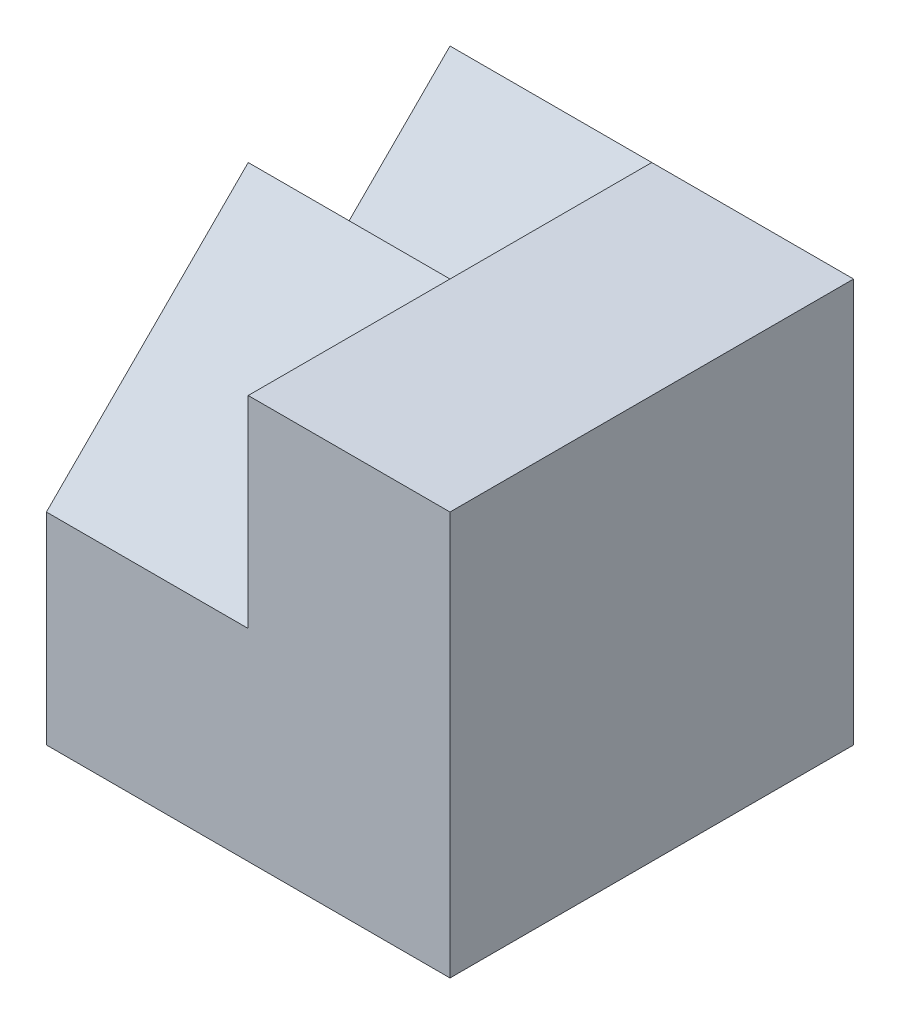
SolidWorks part; units mm, degrees
ref_plane "Front" through (0, 0, 0) normal (0, 0, 1) x (1, 0, 0)
ref_plane "Top" through (0, 0, 0) normal (0, 1, 0) x (1, 0, 0)
ref_plane "Right" through (0, 0, 0) normal (1, 0, 0) x (0, 0, -1)
sketch "Sketch1" plane through (0, 0, 0) normal (0, 1, 0) x (1, 0, 0)
  line L1 (-2, -2) -> (2, -2)
  line L2 (-2, -2) -> (-2, 2)
  line L3 (-2, 2) -> (2, 2)
  line L4 (2, -2) -> (2, 2)
  line L5 (-2, -2) -> (2, 2) construction
  line L6 (-2, 2) -> (2, -2) construction
  point P0 (0, 0)
  dimension "D1" = 4
  dimension "D2" = 4
extrude "Boss-Extrude1" add sketch "Sketch1" along normal blind 4
sketch "Sketch2" plane through (-2, 0, 0) normal (-1, 0, 0) x (0, 0, 1)
  line L0 (2, 2) -> (0, 4)
  line L1 (2, 4) -> (2, 0) construction
  line L2 (-2, 4) -> (2, 4) construction
  line L3 (0, 4) -> (0, 2)
  line L4 (0, 2) -> (-2, 4)
  line L5 (-2, 4) -> (2, 4)
  line L6 (2, 4) -> (2, 2)
  line M2 (2, 0) -> (2, 4)
  line M3 (2, 4) -> (-2, 4)
extrude "Cut-Extrude1" cut sketch "Sketch2" against normal blind 2 contours L4 L3 M3 | L0 M2 M3
